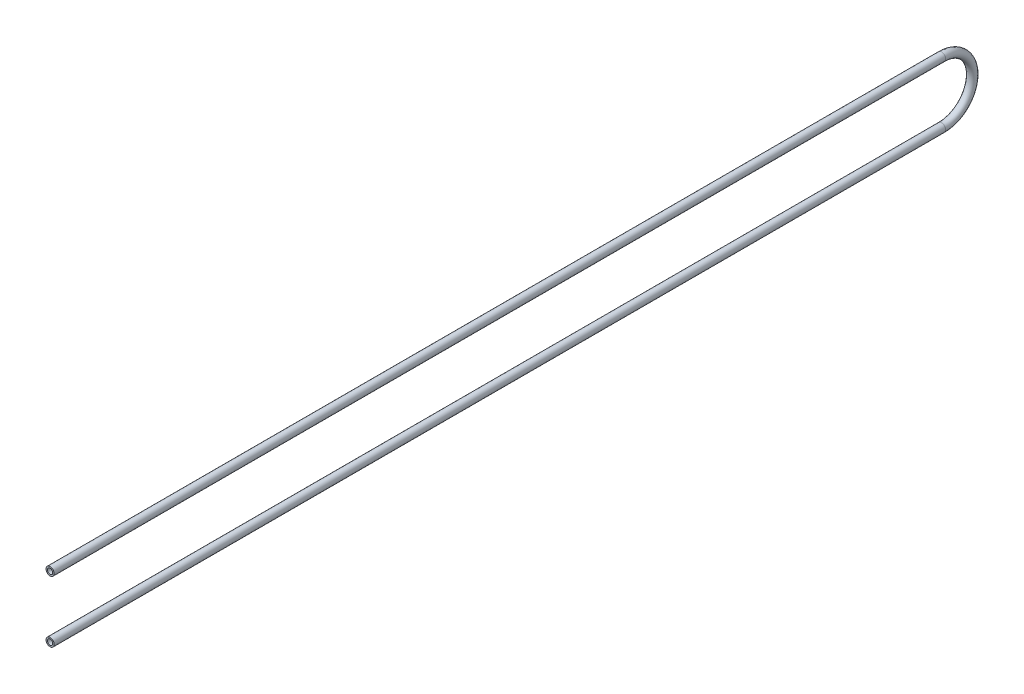
SolidWorks part; units mm, degrees
material "AISI 304"
ref_plane "Front Plane" through (0, 0, 0) normal (0, 0, 1) x (1, 0, 0)
ref_plane "Top Plane" through (0, 0, 0) normal (0, 1, 0) x (1, 0, 0)
ref_plane "Right Plane" through (0, 0, 0) normal (1, 0, 0) x (0, 0, -1)
sketch "Sketch1" plane through (0, 0, 0) normal (1, 0, 0) x (0, 0, -1)
  line L0 (0, 0) -> (0, 80) construction
  line L1 (0, 80) -> (2325, 80)
  line L2 (2325, -80) -> (0, -80)
  arc A0 (2325, 80) -> (2325, -80) centre (2325, 0) cw
  dimension "D1" = 80
  dimension "D2" = 2325
sketch "Sketch2" plane through (0, 0, 0) normal (0, 0, 1) x (1, 0, 0)
  circle A0 centre (0, 80) radius 10.65
  circle A2 centre (0, 80) radius 6.92
  dimension "D1" = 13.84
  dimension "D2" = 21.3
sweep "Sweep1" add profiles "Sketch2" path "Sketch1"
